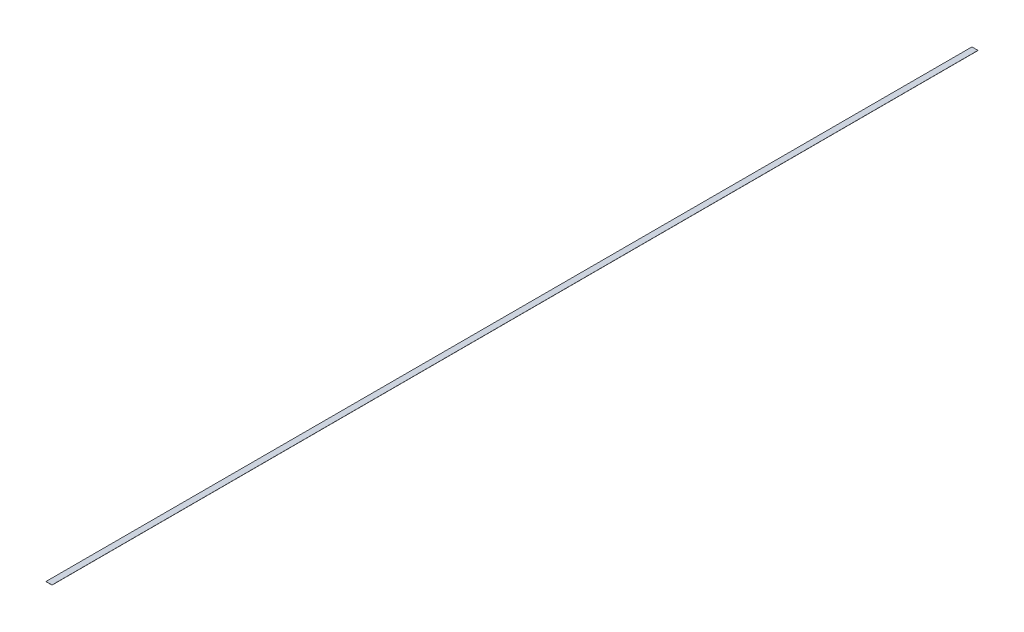
SolidWorks part; units mm, degrees
ref_plane "Front Plane" through (0, 0, 0) normal (0, 0, 1) x (1, 0, 0)
ref_plane "Top Plane" through (0, 0, 0) normal (0, 1, 0) x (1, 0, 0)
ref_plane "Right Plane" through (0, 0, 0) normal (1, 0, 0) x (0, 0, -1)
sketch "Sketch1" plane through (0, 0, 0) normal (0, 1, 0) x (1, 0, 0)
  line L0 (-25.4, 3429) -> (25.4, 3469.1482)
  line L1 (-25.4, -3886.2) -> (25.4, -3886.2)
  line L2 (-25.4, -3886.2) -> (-25.4, 3886.2)
  line L3 (-25.4, 3886.2) -> (25.4, 3886.2)
  line L4 (25.4, -3886.2) -> (25.4, 3886.2)
  line L5 (-25.4, -3886.2) -> (25.4, 3886.2) construction
  line L6 (-25.4, 3886.2) -> (25.4, -3886.2) construction
  point P0 (0, 0)
  dimension "D1" = 50.8
  dimension "D2" = 7772.4
  dimension "D3" = 141.68
  dimension "D4" = 457.2
extrude "Boss-Extrude1" add sketch "Sketch1" along normal blind 1.27 contours L1 L4 L0 L2
